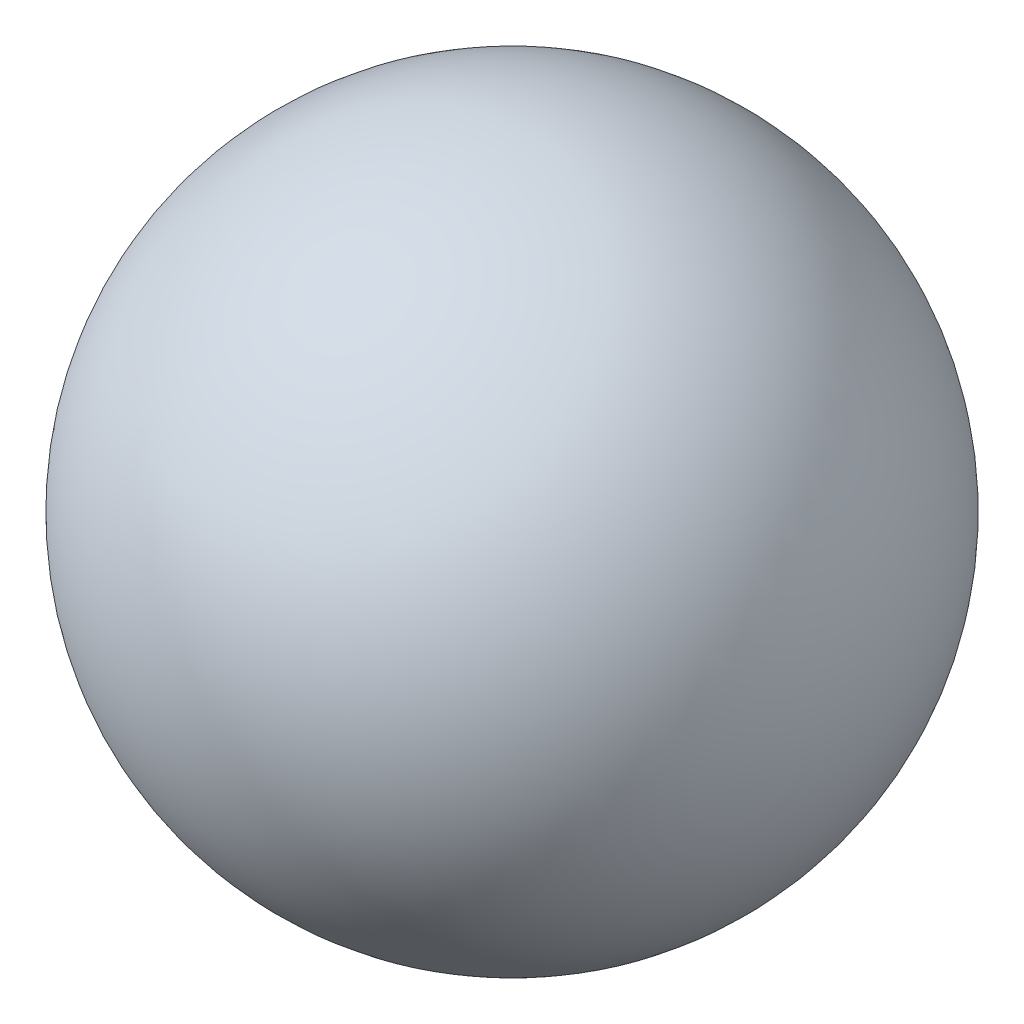
SolidWorks part; units mm, degrees
ref_plane "Front Plane" through (0, 0, 0) normal (0, 0, 1) x (1, 0, 0)
ref_plane "Top Plane" through (0, 0, 0) normal (0, 1, 0) x (1, 0, 0)
ref_plane "Right Plane" through (0, 0, 0) normal (1, 0, 0) x (0, 0, -1)
sketch "Sketch1" plane through (0, 0, 0) normal (0, 0, 1) x (1, 0, 0)
  line L0 (0, 32.8483) -> (0, -9.8517) construction
  line L1 (0, 32.8483) -> (0, -9.8517)
  arc A0 (0, 32.8483) -> (0, -9.8517) centre (0, 11.4983) cw
revolve "Revolve1" add sketch "Sketch1" angle 360 about L0
